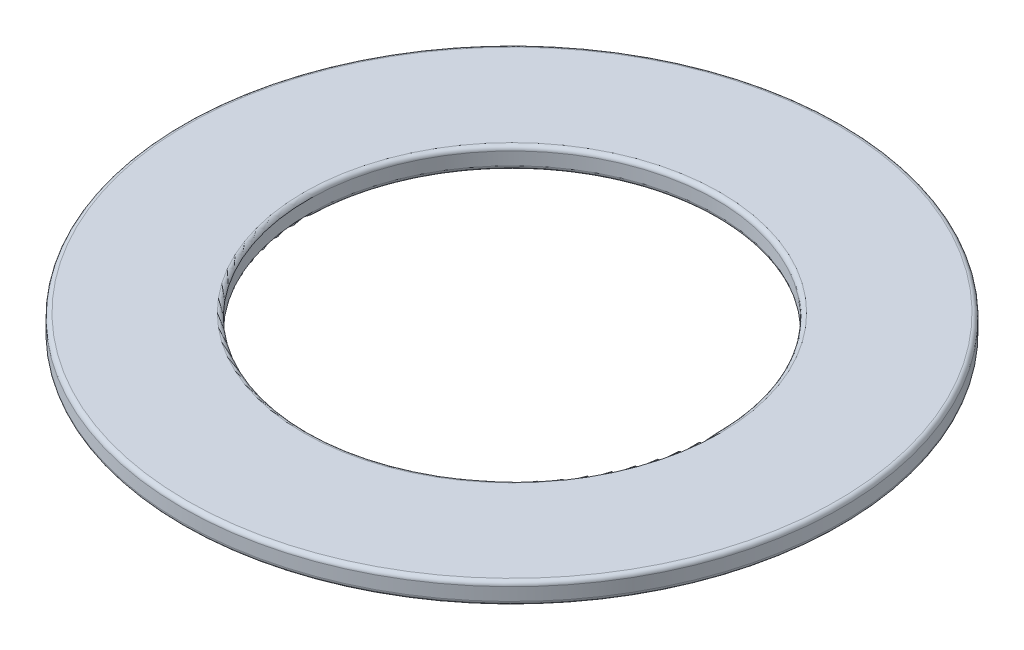
SolidWorks part; units mm, degrees
material "Cast Stainless Steel"
ref_plane "Front Plane" through (0, 0, 0) normal (0, 0, 1) x (1, 0, 0)
ref_plane "Top Plane" through (0, 0, 0) normal (0, 1, 0) x (1, 0, 0)
ref_plane "Right Plane" through (0, 0, 0) normal (1, 0, 0) x (0, 0, -1)
sketch "Sketch2" plane through (0, 0, 0) normal (0, 1, 0) x (1, 0, 0)
  circle A0 centre (0, 0) radius 4.8
  circle A1 centre (0, 0) radius 7.75
  dimension "D1" = 9.6
  dimension "D2" = 15.5
extrude "Boss-Extrude1" add sketch "Sketch2" along normal blind 0.5
fillet "Fillet1" radius 0.1 4 edges at (0, 0, 4.8) (0, 0, 7.75) (0, 0.5, 4.8) (0, 0.5, 7.75)
